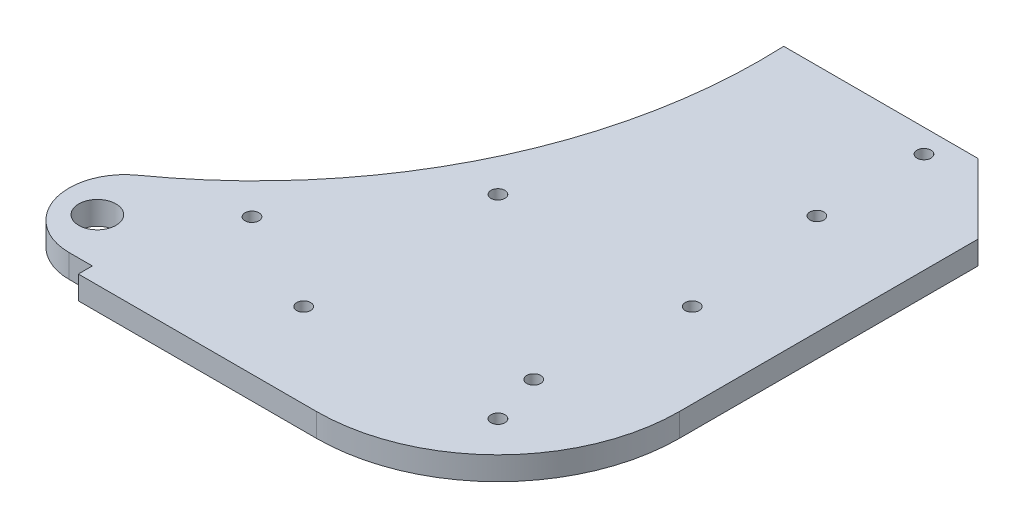
SolidWorks part; units mm, degrees
material "ABS PC"
ref_plane "Plan de face" through (0, 0, 0) normal (0, 0, 1) x (1, 0, 0)
ref_plane "Plan de dessus" through (0, 0, 0) normal (0, 1, 0) x (1, 0, 0)
ref_plane "Plan de droite" through (0, 0, 0) normal (1, 0, 0) x (0, 0, -1)
sketch "Esquisse1" plane through (0, 0, 0) normal (0, 1, 0) x (1, 0, 0)
  line L0 (-56.1, -39) -> (0, -39) construction
  line L1 (39, 0) -> (39, 164.8329) construction
  line L2 (-51.1, -39) -> (0, -39)
  line L3 (39, 0) -> (39, 64.0829)
  line L4 (-51.1, -36) -> (-51.1, -39) construction
  line L5 (-56.1, -36) -> (-51.1, -36) construction
  line L6 (-51.1, -36) -> (-51.1, -39)
  line L7 (-56.1, -36) -> (-51.1, -36)
  line L8 (-17.7153, 79.0829) -> (24, 79.0829)
  line L10 (12.4, 79.0829) -> (22.4, 79.0829) construction
  line L11 (24, 79.0829) -> (39, 64.0829)
  arc A0 (0, -39) -> (39, 0) centre (0, 0) ccw construction
  arc A2 (0, -39) -> (39, 0) centre (0, 0) ccw
  arc A3 (-63.071, -14.2324) -> (-189.129, -14.2324) centre (-126.1, 74.0829) ccw construction
  arc A4 (-63.071, -14.2324) -> (-17.7153, 79.0829) centre (-126.1, 74.0829) ccw
  arc A6 (-63.071, -14.2324) -> (-56.1, -36) centre (-56.1, -24) ccw
  arc A7 (-63.071, -14.2324) -> (-56.1, -36) centre (-56.1, -24) ccw construction
  point P13 (39, 79.0829)
extrude "Boss.-Extru.1" add sketch "Esquisse1" along normal blind 5
sketch "Esquisse2" plane through (0, 0, 0) normal (0, -1, 0) x (1, 0, 0)
  circle A0 centre (20.8597, 20.8597) radius 1.5
  circle A1 centre (20.8597, -20.8597) radius 1.5
  circle A2 centre (-20.8597, -20.8597) radius 1.5
  circle A3 centre (-20.8597, 20.8597) radius 1.5
  circle A4 centre (17.4, -74.0829) radius 1.5
  circle A5 centre (17.4, 9.7171) radius 1.5
  dimension "D1" = 3
extrude "Enlèv. mat.-Extru.1" cut sketch "Esquisse2" against normal through all
sketch "Esquisse3" plane through (0, 5, 0) normal (0, 1, 0) x (1, 0, 0)
  line L0 (17.4, 51.0829) -> (22.4, 51.0829) construction
  line L1 (-43.1, -9.7171) -> (-43.1, -14.7171) construction
  line L2 (22.4, 52.5829) -> (22.4, 49.5829) construction
  line L3 (-41.6, -14.7171) -> (-44.6, -14.7171) construction
  circle A0 centre (17.4, 51.0829) radius 1.5
  circle A1 centre (-43.1, -9.7171) radius 1.5
  dimension "D1" = 3
  dimension "D2" = 5
extrude "Enlèv. mat.-Extru.2" cut sketch "Esquisse3" against normal through all
sketch "Esquisse4" plane through (0, 5, 0) normal (0, 1, 0) x (1, 0, 0)
  circle A0 centre (-60.1, -25.9171) radius 4
  circle A1 centre (-60.1, -25.9171) radius 4 construction
extrude "Enlèv. mat.-Extru.3" cut sketch "Esquisse4" against normal through all
